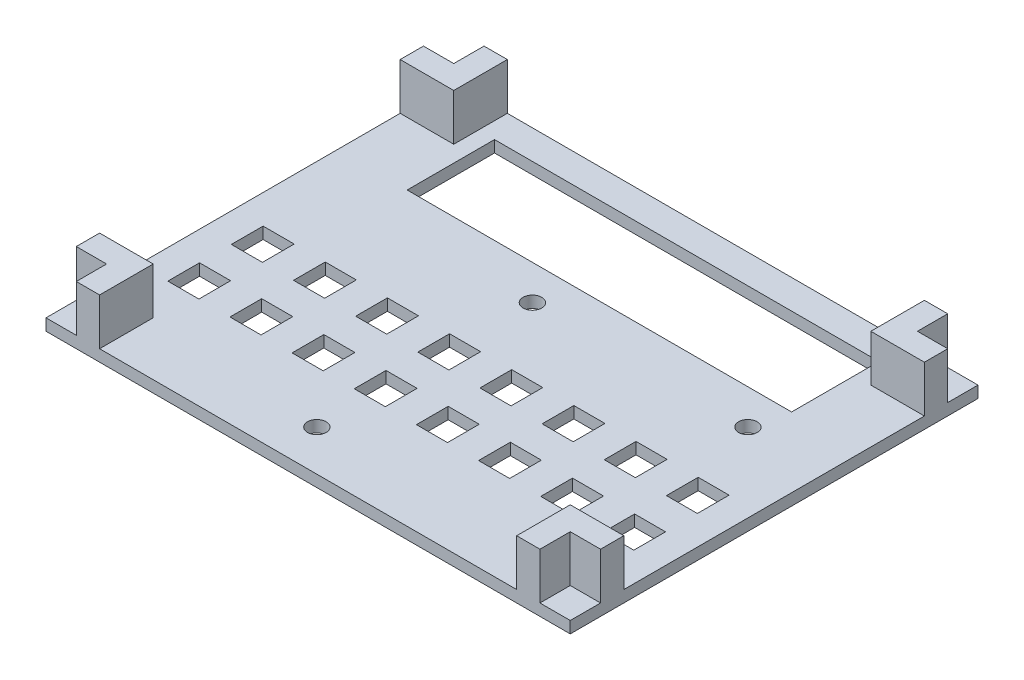
SolidWorks part; units mm, degrees
ref_plane "Plano frontal" through (0, 0, 0) normal (0, 0, 1) x (1, 0, 0)
ref_plane "Plano superior" through (0, 0, 0) normal (0, 1, 0) x (1, 0, 0)
ref_plane "Plano direito" through (0, 0, 0) normal (1, 0, 0) x (0, 0, -1)
sketch "Esboço1" plane through (0, 0, 0) normal (0, 1, 0) x (1, 0, 0)
  line L1 (-45, -35) -> (45, -35)
  line L2 (-45, -35) -> (-45, 35)
  line L3 (-45, 35) -> (45, 35)
  line L4 (45, -35) -> (45, 35)
  line L5 (-45, -35) -> (45, 35) construction
  line L6 (-45, 35) -> (45, -35) construction
  point P0 (0, 0)
  dimension "D1" = 90
  dimension "D2" = 70
extrude "Ressalto-extrusão1" add sketch "Esboço1" along normal blind 2
sketch "Esboço2" plane through (0, 2, 0) normal (0, 1, 0) x (1, 0, 0)
  line L7 (-40, 30) -> (-34.666, 30)
  line L10 (-45, 35) -> (-45, -35) construction
  line L11 (-40, -30) -> (40, -30)
  line L12 (-40, -30) -> (-40, 30)
  line L13 (-40, 30) -> (40, 30)
  line L14 (40, -30) -> (40, 30)
  line L15 (-40, -30) -> (40, 30) construction
  line L16 (-40, 30) -> (40, -30) construction
  line L17 (45, 35) -> (-45, 35) construction
  line L18 (-40, 30) -> (-40, 24.55)
  line L19 (-40, 24.55) -> (-34.666, 24.55)
  line L20 (-34.666, 30) -> (-34.666, 24.55)
  line L104 (-29.33, -2.73) -> (-29.33, -8.18)
  line L105 (-23.996, -2.73) -> (-23.996, -8.18)
  line L106 (-29.33, -2.73) -> (-23.996, -2.73)
  line L107 (-29.33, -8.18) -> (-23.996, -8.18)
  line L108 (-18.66, -2.73) -> (-18.66, -8.18)
  line L109 (-13.326, -2.73) -> (-13.326, -8.18)
  line L110 (-18.66, -2.73) -> (-13.326, -2.73)
  line L111 (-18.66, -8.18) -> (-13.326, -8.18)
  line L112 (-7.99, -2.73) -> (-7.99, -8.18)
  line L113 (-2.656, -2.73) -> (-2.656, -8.18)
  line L114 (-7.99, -2.73) -> (-2.656, -2.73)
  line L115 (-7.99, -8.18) -> (-2.656, -8.18)
  line L116 (2.68, -2.73) -> (2.68, -8.18)
  line L117 (8.014, -2.73) -> (8.014, -8.18)
  line L118 (2.68, -2.73) -> (8.014, -2.73)
  line L119 (2.68, -8.18) -> (8.014, -8.18)
  line L120 (13.35, -2.73) -> (13.35, -8.18)
  line L121 (18.684, -2.73) -> (18.684, -8.18)
  line L122 (13.35, -2.73) -> (18.684, -2.73)
  line L123 (13.35, -8.18) -> (18.684, -8.18)
  line L124 (24.02, -2.73) -> (24.02, -8.18)
  line L125 (29.354, -2.73) -> (29.354, -8.18)
  line L126 (24.02, -2.73) -> (29.354, -2.73)
  line L127 (24.02, -8.18) -> (29.354, -8.18)
  line L128 (34.69, -2.73) -> (34.69, -8.18)
  line L129 (40.024, -2.73) -> (40.024, -8.18)
  line L130 (34.69, -2.73) -> (40.024, -2.73)
  line L131 (34.69, -8.18) -> (40.024, -8.18)
  line L132 (-29.33, -13.64) -> (-29.33, -19.09)
  line L133 (-23.996, -13.64) -> (-23.996, -19.09)
  line L134 (-29.33, -13.64) -> (-23.996, -13.64)
  line L135 (-29.33, -19.09) -> (-23.996, -19.09)
  line L136 (-18.66, -13.64) -> (-18.66, -19.09)
  line L137 (-13.326, -13.64) -> (-13.326, -19.09)
  line L138 (-18.66, -13.64) -> (-13.326, -13.64)
  line L139 (-18.66, -19.09) -> (-13.326, -19.09)
  line L140 (-7.99, -13.64) -> (-7.99, -19.09)
  line L141 (-2.656, -13.64) -> (-2.656, -19.09)
  line L142 (-7.99, -13.64) -> (-2.656, -13.64)
  line L143 (-7.99, -19.09) -> (-2.656, -19.09)
  line L144 (2.68, -13.64) -> (2.68, -19.09)
  line L145 (8.014, -13.64) -> (8.014, -19.09)
  line L146 (2.68, -13.64) -> (8.014, -13.64)
  line L147 (2.68, -19.09) -> (8.014, -19.09)
  line L148 (13.35, -13.64) -> (13.35, -19.09)
  line L149 (18.684, -13.64) -> (18.684, -19.09)
  line L150 (13.35, -13.64) -> (18.684, -13.64)
  line L151 (13.35, -19.09) -> (18.684, -19.09)
  line L152 (24.02, -13.64) -> (24.02, -19.09)
  line L153 (29.354, -13.64) -> (29.354, -19.09)
  line L154 (24.02, -13.64) -> (29.354, -13.64)
  line L155 (24.02, -19.09) -> (29.354, -19.09)
  line L156 (34.69, -13.64) -> (34.69, -19.09)
  line L157 (40.024, -13.64) -> (40.024, -19.09)
  line L158 (34.69, -13.64) -> (40.024, -13.64)
  line L159 (34.69, -19.09) -> (40.024, -19.09)
  line L196 (-40, -2.73) -> (-40, -8.18)
  line L197 (-34.666, -2.73) -> (-34.666, -8.18)
  line L198 (-40, -2.73) -> (-34.666, -2.73)
  line L199 (-40, -8.18) -> (-34.666, -8.18)
  line L200 (-40, -13.64) -> (-40, -19.09)
  line L201 (-34.666, -13.64) -> (-34.666, -19.09)
  line L202 (-40, -13.64) -> (-34.666, -13.64)
  line L203 (-40, -19.09) -> (-34.666, -19.09)
  line L208 (-29.33, 30) -> (-29.33, 24.55) [skipped]
  line L209 (-23.996, 30) -> (-23.996, 24.55) [skipped]
  line L210 (-29.33, 30) -> (-23.996, 30) [skipped]
  line L211 (-29.33, 24.55) -> (-23.996, 24.55) [skipped]
  line L212 (-18.66, 30) -> (-18.66, 24.55) [skipped]
  line L213 (-13.326, 30) -> (-13.326, 24.55) [skipped]
  line L214 (-18.66, 30) -> (-13.326, 30) [skipped]
  line L215 (-18.66, 24.55) -> (-13.326, 24.55) [skipped]
  line L216 (-7.99, 30) -> (-7.99, 24.55) [skipped]
  line L217 (-2.656, 30) -> (-2.656, 24.55) [skipped]
  line L218 (-7.99, 30) -> (-2.656, 30) [skipped]
  line L219 (-7.99, 24.55) -> (-2.656, 24.55) [skipped]
  line L220 (2.68, 30) -> (2.68, 24.55) [skipped]
  line L221 (8.014, 30) -> (8.014, 24.55) [skipped]
  line L222 (2.68, 30) -> (8.014, 30) [skipped]
  line L223 (2.68, 24.55) -> (8.014, 24.55) [skipped]
  line L224 (13.35, 30) -> (13.35, 24.55) [skipped]
  line L225 (18.684, 30) -> (18.684, 24.55) [skipped]
  line L226 (13.35, 30) -> (18.684, 30) [skipped]
  line L227 (13.35, 24.55) -> (18.684, 24.55) [skipped]
  line L228 (24.02, 30) -> (24.02, 24.55) [skipped]
  line L229 (29.354, 30) -> (29.354, 24.55) [skipped]
  line L230 (24.02, 30) -> (29.354, 30) [skipped]
  line L231 (24.02, 24.55) -> (29.354, 24.55) [skipped]
  line L232 (34.69, 30) -> (34.69, 24.55) [skipped]
  line L233 (40.024, 30) -> (40.024, 24.55) [skipped]
  line L234 (34.69, 30) -> (40.024, 30) [skipped]
  line L235 (34.69, 24.55) -> (40.024, 24.55) [skipped]
  line L236 (-29.33, 19.09) -> (-29.33, 13.64) [skipped]
  line L237 (-23.996, 19.09) -> (-23.996, 13.64) [skipped]
  line L238 (-29.33, 19.09) -> (-23.996, 19.09) [skipped]
  line L239 (-29.33, 13.64) -> (-23.996, 13.64) [skipped]
  line L240 (-18.66, 19.09) -> (-18.66, 13.64) [skipped]
  line L241 (-13.326, 19.09) -> (-13.326, 13.64) [skipped]
  line L242 (-18.66, 19.09) -> (-13.326, 19.09) [skipped]
  line L243 (-18.66, 13.64) -> (-13.326, 13.64) [skipped]
  line L244 (-7.99, 19.09) -> (-7.99, 13.64) [skipped]
  line L245 (-2.656, 19.09) -> (-2.656, 13.64) [skipped]
  line L246 (-7.99, 19.09) -> (-2.656, 19.09) [skipped]
  line L247 (-7.99, 13.64) -> (-2.656, 13.64) [skipped]
  line L248 (2.68, 19.09) -> (2.68, 13.64) [skipped]
  line L249 (8.014, 19.09) -> (8.014, 13.64) [skipped]
  line L250 (2.68, 19.09) -> (8.014, 19.09) [skipped]
  line L251 (2.68, 13.64) -> (8.014, 13.64) [skipped]
  line L252 (13.35, 19.09) -> (13.35, 13.64) [skipped]
  line L253 (18.684, 19.09) -> (18.684, 13.64) [skipped]
  line L254 (13.35, 19.09) -> (18.684, 19.09) [skipped]
  line L255 (13.35, 13.64) -> (18.684, 13.64) [skipped]
  line L256 (24.02, 19.09) -> (24.02, 13.64) [skipped]
  line L257 (29.354, 19.09) -> (29.354, 13.64) [skipped]
  line L258 (24.02, 19.09) -> (29.354, 19.09) [skipped]
  line L259 (24.02, 13.64) -> (29.354, 13.64) [skipped]
  line L260 (34.69, 19.09) -> (34.69, 13.64) [skipped]
  line L261 (40.024, 19.09) -> (40.024, 13.64) [skipped]
  line L262 (34.69, 19.09) -> (40.024, 19.09) [skipped]
  line L263 (34.69, 13.64) -> (40.024, 13.64) [skipped]
  line L264 (-40, 19.09) -> (-40, 13.64) [skipped]
  line L265 (-34.666, 19.09) -> (-34.666, 13.64) [skipped]
  line L266 (-40, 19.09) -> (-34.666, 19.09) [skipped]
  line L267 (-40, 13.64) -> (-34.666, 13.64) [skipped]
  line L268 (-40, -24.55) -> (-40, -30) [skipped]
  line L269 (-34.666, -24.55) -> (-34.666, -30) [skipped]
  line L270 (-40, -24.55) -> (-34.666, -24.55) [skipped]
  line L271 (-40, -30) -> (-34.666, -30) [skipped]
  line L272 (34.69, -24.55) -> (34.69, -30) [skipped]
  line L273 (40.024, -24.55) -> (40.024, -30) [skipped]
  line L274 (34.69, -24.55) -> (40.024, -24.55) [skipped]
  line L275 (34.69, -30) -> (40.024, -30) [skipped]
  line L276 (-29.33, 8.18) -> (-29.33, 2.73) [skipped]
  line L277 (-23.996, 8.18) -> (-23.996, 2.73) [skipped]
  line L278 (-29.33, 8.18) -> (-23.996, 8.18) [skipped]
  line L279 (-29.33, 2.73) -> (-23.996, 2.73) [skipped]
  line L280 (-18.66, 8.18) -> (-18.66, 2.73) [skipped]
  line L281 (-13.326, 8.18) -> (-13.326, 2.73) [skipped]
  line L282 (-18.66, 8.18) -> (-13.326, 8.18) [skipped]
  line L283 (-18.66, 2.73) -> (-13.326, 2.73) [skipped]
  line L284 (-7.99, 8.18) -> (-7.99, 2.73) [skipped]
  line L285 (-2.656, 8.18) -> (-2.656, 2.73) [skipped]
  line L286 (-7.99, 8.18) -> (-2.656, 8.18) [skipped]
  line L287 (-7.99, 2.73) -> (-2.656, 2.73) [skipped]
  line L288 (2.68, 8.18) -> (2.68, 2.73) [skipped]
  line L289 (8.014, 8.18) -> (8.014, 2.73) [skipped]
  line L290 (2.68, 8.18) -> (8.014, 8.18) [skipped]
  line L291 (2.68, 2.73) -> (8.014, 2.73) [skipped]
  line L292 (13.35, 8.18) -> (13.35, 2.73) [skipped]
  line L293 (18.684, 8.18) -> (18.684, 2.73) [skipped]
  line L294 (13.35, 8.18) -> (18.684, 8.18) [skipped]
  line L295 (13.35, 2.73) -> (18.684, 2.73) [skipped]
  line L296 (24.02, 8.18) -> (24.02, 2.73) [skipped]
  line L297 (29.354, 8.18) -> (29.354, 2.73) [skipped]
  line L298 (24.02, 8.18) -> (29.354, 8.18) [skipped]
  line L299 (24.02, 2.73) -> (29.354, 2.73) [skipped]
  line L300 (34.69, 8.18) -> (34.69, 2.73) [skipped]
  line L301 (40.024, 8.18) -> (40.024, 2.73) [skipped]
  line L302 (34.69, 8.18) -> (40.024, 8.18) [skipped]
  line L303 (34.69, 2.73) -> (40.024, 2.73) [skipped]
  line L304 (-40, 8.18) -> (-40, 2.73) [skipped]
  line L305 (-34.666, 8.18) -> (-34.666, 2.73) [skipped]
  line L306 (-40, 8.18) -> (-34.666, 8.18) [skipped]
  line L307 (-40, 2.73) -> (-34.666, 2.73) [skipped]
  line L308 (-29.33, -24.55) -> (-29.33, -30) [skipped]
  line L309 (-23.996, -24.55) -> (-23.996, -30) [skipped]
  line L310 (-29.33, -24.55) -> (-23.996, -24.55) [skipped]
  line L311 (-29.33, -30) -> (-23.996, -30) [skipped]
  line L312 (-18.66, -24.55) -> (-18.66, -30) [skipped]
  line L313 (-13.326, -24.55) -> (-13.326, -30) [skipped]
  line L314 (-18.66, -24.55) -> (-13.326, -24.55) [skipped]
  line L315 (-18.66, -30) -> (-13.326, -30) [skipped]
  line L316 (-7.99, -24.55) -> (-7.99, -30) [skipped]
  line L317 (-2.656, -24.55) -> (-2.656, -30) [skipped]
  line L318 (-7.99, -24.55) -> (-2.656, -24.55) [skipped]
  line L319 (-7.99, -30) -> (-2.656, -30) [skipped]
  line L320 (2.68, -24.55) -> (2.68, -30) [skipped]
  line L321 (8.014, -24.55) -> (8.014, -30) [skipped]
  line L322 (2.68, -24.55) -> (8.014, -24.55) [skipped]
  line L323 (2.68, -30) -> (8.014, -30) [skipped]
  line L324 (13.35, -24.55) -> (13.35, -30) [skipped]
  line L325 (18.684, -24.55) -> (18.684, -30) [skipped]
  line L326 (13.35, -24.55) -> (18.684, -24.55) [skipped]
  line L327 (13.35, -30) -> (18.684, -30) [skipped]
  line L328 (24.02, -24.55) -> (24.02, -30) [skipped]
  line L329 (29.354, -24.55) -> (29.354, -30) [skipped]
  line L330 (24.02, -24.55) -> (29.354, -24.55) [skipped]
  line L331 (24.02, -30) -> (29.354, -30) [skipped]
  point P0 (0, 0)
  dimension "D1" = 5
  dimension "D2" = 5
  dimension "D3" = 5.334
  dimension "D4" = 5.45
  dimension "D5" = 6
sketch "Esboço3" plane through (0, 2, 0) normal (0, 1, 0) x (1, 0, 0)
  line L5 (-45, 35) -> (-35.8, 35)
  line L6 (-45, 35) -> (-45, 25.8)
  line L7 (-45, 25.8) -> (-35.8, 25.8)
  line L8 (-35.8, 35) -> (-35.8, 25.8)
  line L33 (-45, 35) -> (-39.8, 35)
  line L34 (-45, 35) -> (-45, 29.8)
  line L35 (-45, 29.8) -> (-39.8, 29.8)
  line L36 (-39.8, 35) -> (-39.8, 29.8)
  line L37 (45, 35) -> (39.8, 35)
  line L38 (45, 35) -> (45, 29.8)
  line L39 (45, 29.8) -> (39.8, 29.8)
  line L40 (39.8, 35) -> (39.8, 29.8)
  line L41 (45, 35) -> (35.8, 35)
  line L42 (45, 35) -> (45, 25.8)
  line L43 (45, 25.8) -> (35.8, 25.8)
  line L44 (35.8, 35) -> (35.8, 25.8)
  line L45 (45, -35) -> (39.8, -35)
  line L46 (45, -35) -> (45, -29.8)
  line L47 (45, -29.8) -> (39.8, -29.8)
  line L48 (39.8, -35) -> (39.8, -29.8)
  line L49 (45, -35) -> (35.8, -35)
  line L50 (45, -35) -> (45, -25.8)
  line L51 (45, -25.8) -> (35.8, -25.8)
  line L52 (35.8, -35) -> (35.8, -25.8)
  line L53 (-45, -35) -> (-39.8, -35)
  line L54 (-45, -35) -> (-45, -29.8)
  line L55 (-45, -29.8) -> (-39.8, -29.8)
  line L56 (-39.8, -35) -> (-39.8, -29.8)
  line L57 (-45, -35) -> (-35.8, -35)
  line L58 (-45, -35) -> (-45, -25.8)
  line L59 (-45, -25.8) -> (-35.8, -25.8)
  line L60 (-35.8, -35) -> (-35.8, -25.8)
  line M17 (45, -35) -> (45, 35)
  line M18 (45, 35) -> (-45, 35)
  line M19 (-45, 35) -> (-45, -35)
  line M20 (-45, -35) -> (45, -35)
  dimension "D1" = 4
  dimension "D2" = 4
  dimension "D3" = 5.2
  dimension "D4" = 5.2
  dimension "D5" = 5.2
  dimension "D6" = 4
  dimension "D7" = 4
  dimension "D8" = 4
  dimension "D9" = 5.2
  dimension "D10" = 5.2
  dimension "D11" = 4
  dimension "D12" = 5.2
  dimension "D13" = 4
  dimension "D14" = 4
  dimension "D15" = 5.2
extrude "Ressalto-extrusão4" add sketch "Esboço3" along normal blind 8 contours L60 L59 L55 L56 M20 M19 | L52 L48 L47 L51 M20 M17 | L44 L43 L39 L40 M18 M17 | L36 L35 L6 L7 L8 M18
sketch "Esboço6" plane through (0, 0, 0) normal (0, -1, 0) x (1, 0, 0)
  line L0 (0, 0) -> (0, -35) construction
  line L1 (45, -35) -> (-45, -35) construction
  line L3 (33, -30) -> (-33, -30)
  line L4 (33, -30) -> (33, -15)
  line L5 (33, -15) -> (-33, -15)
  line L6 (-33, -30) -> (-33, -15)
  line L7 (33, -30) -> (-33, -15) construction
  line L8 (33, -15) -> (-33, -30) construction
  point P5 (0, -22.5)
  dimension "D1" = 15
  dimension "D2" = 66
  dimension "D3" = 5
extrude "Corte-extrusão4" cut sketch "Esboço6" against normal blind 3
extrude "Corte-extrusão6" cut sketch "Esboço2" against normal blind 5 contours L12 L203 L201 L202 | L12 L199 L197 L198 | L132 L135 L133 L134 | L104 L107 L105 L106 | L136 L139 L137 L138 | L108 L111 L109 L110 | L140 L143 L141 L142 | L112 L115 L113 L114 | L144 L147 L145 L146 | L116 L119 L117 L118 | L148 L151 L149 L150 | L120 L123 L121 L122 | L152 L155 L153 L154 | L124 L127 L125 L126 | L156 L159 L14 L158 | L128 L131 L14 L130
sketch "Esboço7" plane through (0, 2, 0) normal (0, 1, 0) x (1, 0, 0)
  line L1 (45, -25.8) -> (45, 25.8) construction
  line L3 (35.8, 35) -> (-35.8, 35) construction
  line L4 (31.5, 9) -> (-5.5, 9) construction
  line L5 (-5.5, 9) -> (-5.5, -28) construction
  line L6 (-5.5, -28) -> (31.5, -28) construction
  line L7 (31.5, -28) -> (31.5, 9) construction
  circle A0 centre (31.5, 9) radius 1.6
  circle A1 centre (-5.5, 9) radius 1.6
  circle A2 centre (-5.5, -28) radius 1.6
  circle A3 centre (31.5, -28) radius 1.6
  dimension "D1" = 3.2
  dimension "D6" = 3.2
  dimension "D7" = 3.2
  dimension "D8" = 3.2
  dimension "D2" = 13.5
  dimension "D3" = 26
  dimension "D4" = 37
  dimension "D5" = 37
extrude "Corte-extrusão7" cut sketch "Esboço7" against normal blind 3
